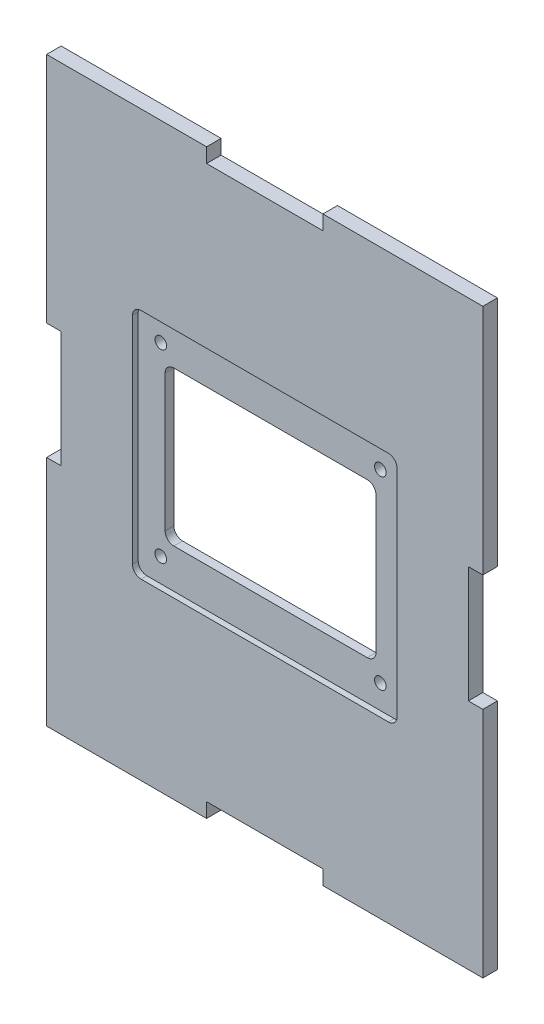
SolidWorks part; units mm, degrees
ref_plane "Alzado" through (0, 0, 0) normal (0, 0, 1) x (1, 0, 0)
ref_plane "Planta" through (0, 0, 0) normal (0, 1, 0) x (1, 0, 0)
ref_plane "Vista lateral" through (0, 0, 0) normal (1, 0, 0) x (0, 0, -1)
sketch "Croquis1" plane through (0, 0, 0) normal (0, 0, 1) x (1, 0, 0)
  line L1 (-75, -100) -> (75, -100)
  line L2 (-75, -100) -> (-75, 100)
  line L3 (-75, 100) -> (75, 100)
  line L4 (75, -100) -> (75, 100)
  line L5 (-75, -100) -> (75, 100) construction
  line L6 (-75, 100) -> (75, -100) construction
  dimension "D1" = 150
extrude "Saliente-Extruir1" add sketch "Croquis1" along normal blind 5
sketch "Croquis3" plane through (0, 0, 5) normal (0, 0, 1) x (1, 0, 0)
  line L0 (75, 100) -> (-75, 100) construction
  line L1 (20, 100) -> (-20, 100)
  line L2 (20, 100) -> (20, 95)
  line L3 (20, 95) -> (-20, 95)
  line L4 (-20, 100) -> (-20, 95)
  line L5 (-75, 0) -> (75, 0) construction
  line L6 (-75, 100) -> (-75, -100) construction
  line L7 (75, -100) -> (75, 100) construction
  line L8 (-20, -100) -> (-20, -95)
  line L9 (20, -95) -> (-20, -95)
  line L10 (20, -100) -> (20, -95)
  line L11 (20, -100) -> (-20, -100)
  line L12 (0, 0) -> (0, 37.5115) construction
  line L13 (-75, -20) -> (-70, -20)
  line L14 (-75, -20) -> (-75, 20)
  line L15 (-75, 20) -> (-70, 20)
  line L16 (-70, -20) -> (-70, 20)
  line L17 (70, -20) -> (70, 20)
  line L18 (75, 20) -> (70, 20)
  line L19 (75, -20) -> (75, 20)
  line L20 (75, -20) -> (70, -20)
  line L22 (-36.25, -26.5) -> (36.25, -26.5)
  line L23 (-36.25, -26.5) -> (-36.25, 26.5)
  line L24 (-36.25, 26.5) -> (36.25, 26.5)
  line L25 (36.25, -26.5) -> (36.25, 26.5)
  line L26 (-36.25, -26.5) -> (36.25, 26.5) construction
  line L27 (-36.25, 26.5) -> (36.25, -26.5) construction
  circle A0 centre (-37.75, 31.8) radius 2
  circle A1 centre (37.75, 31.8) radius 2
  circle A2 centre (37.75, -31.8) radius 2
  circle A3 centre (-37.75, -31.8) radius 2
  point P6 (0, 100)
  point P7 (0, 100)
  point P23 (-75, 0)
  dimension "D7" = 37.75
  dimension "D1" = 40
  dimension "D2" = 5
  dimension "D3" = 5
  dimension "D4" = 40
  dimension "D5" = 72.5
  dimension "D6" = 53
  dimension "D8" = 31.8
extrude "Cortar-Extruir2" cut sketch "Croquis3" against normal up to vertex (5 mm away)
sketch "Croquis4" plane through (0, 0, 5) normal (0, 0, 1) x (1, 0, 0)
  line L1 (45.5, -40) -> (-45.5, -40)
  line L2 (45.5, -40) -> (45.5, 40)
  line L3 (45.5, 40) -> (-45.5, 40)
  line L4 (-45.5, -40) -> (-45.5, 40)
  line L5 (45.5, -40) -> (-45.5, 40) construction
  line L6 (45.5, 40) -> (-45.5, -40) construction
  point P0 (0, 0)
  dimension "D1" = 91
  dimension "D2" = 80
extrude "Cortar-Extruir3" cut sketch "Croquis4" against normal blind 2
fillet "Redondeo1" radius 3 8 edges at (-36.25, -26.5, 1.5) (-45.5, -40, 4) (36.25, -26.5, 1.5) (45.5, -40, 4) (36.25, 26.5, 1.5) (45.5, 40, 4) (-45.5, 40, 4) (-36.25, 26.5, 1.5)
